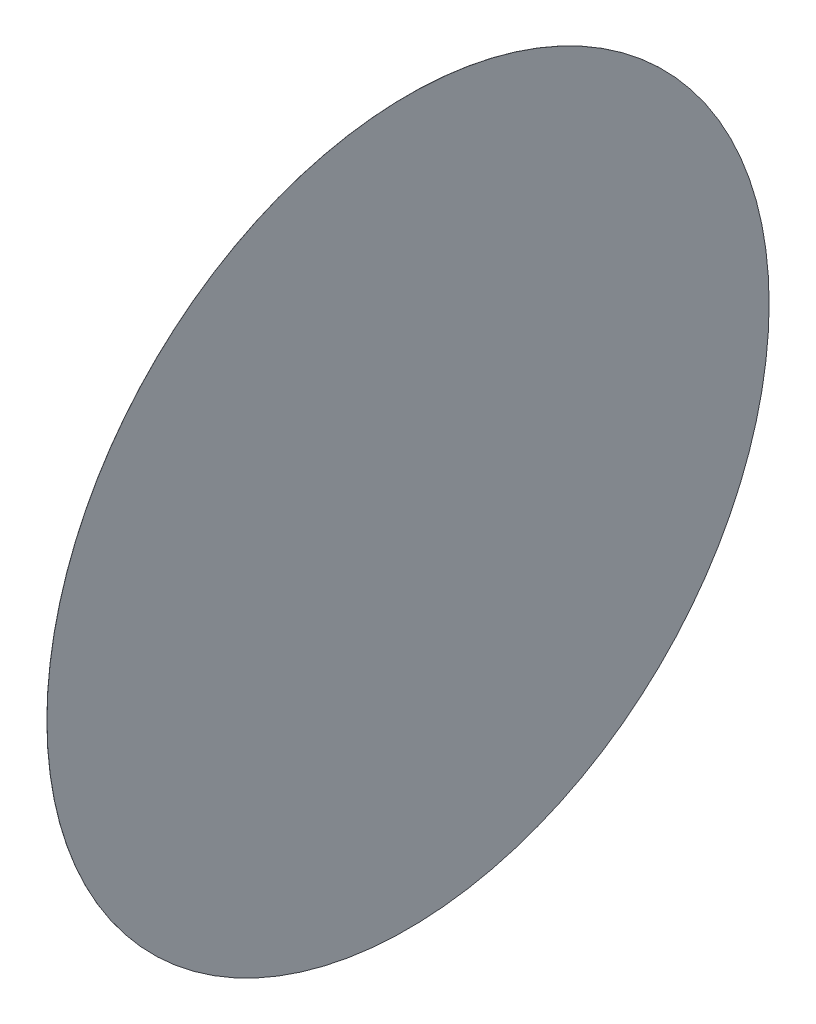
SolidWorks part; units mm, degrees
ref_plane "Front Plane" through (0, 0, 0) normal (0, 0, 1) x (1, 0, 0)
ref_plane "Top Plane" through (0, 0, 0) normal (0, 1, 0) x (1, 0, 0)
ref_plane "Right Plane" through (0, 0, 0) normal (1, 0, 0) x (0, 0, -1)
sketch "Sketch1" plane through (0, 0, 0) normal (1, 0, 0) x (0, 0, -1)
  circle A0 centre (0, 0) radius 4
extrude "Boss-Extrude1" add sketch "Sketch1" along normal blind 0.001
